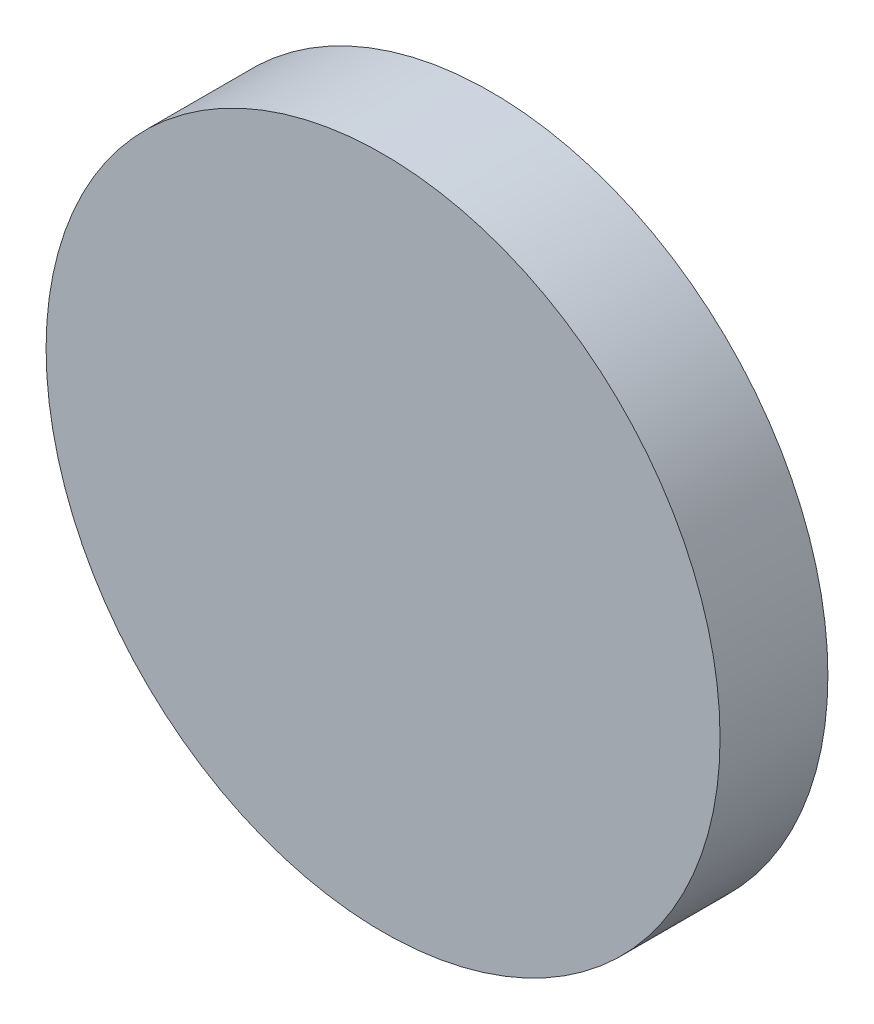
SolidWorks part; units mm, degrees
ref_plane "Спереди" through (0, 0, 0) normal (0, 0, 1) x (1, 0, 0)
ref_plane "Сверху" through (0, 0, 0) normal (0, 1, 0) x (1, 0, 0)
ref_plane "Справа" through (0, 0, 0) normal (1, 0, 0) x (0, 0, -1)
sketch "Эскиз1" plane through (0, 0, 0) normal (0, 0, 1) x (1, 0, 0)
  circle A0 centre (0, 0) radius 12.5
  dimension "D1" = 25
extrude "Бобышка-Вытянуть1" add sketch "Эскиз1" along normal blind 4 contours A0
